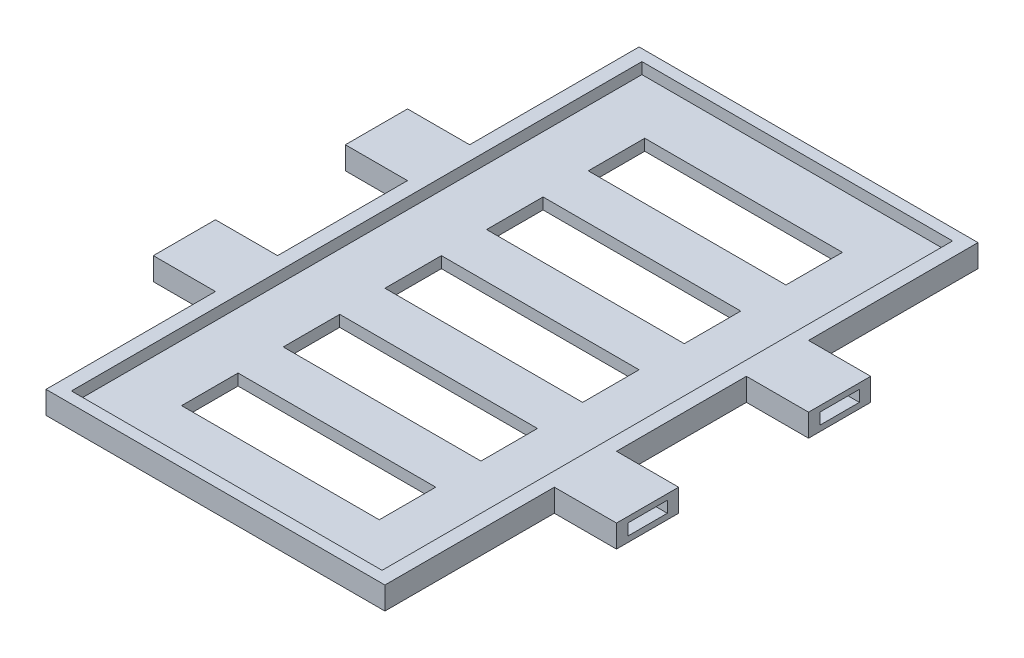
SolidWorks part; units mm, degrees
ref_plane "Alzado" through (0, 0, 0) normal (0, 0, 1) x (1, 0, 0)
ref_plane "Planta" through (0, 0, 0) normal (0, 1, 0) x (1, 0, 0)
ref_plane "Vista lateral" through (0, 0, 0) normal (1, 0, 0) x (0, 0, -1)
sketch "Croquis1" plane through (0, 0, 0) normal (0, 1, 0) x (1, 0, 0)
  line L0 (30, -52.5) -> (30, -22.5)
  line L1 (-30, 52.5) -> (30, 52.5)
  line L2 (30, -22.5) -> (30, -11.5) construction
  line L3 (-30, -52.5) -> (30, -52.5)
  line L4 (30, 11.5) -> (30, 22.5) construction
  line L5 (-30, 52.5) -> (30, -52.5) construction
  line L6 (-30, -52.5) -> (30, 52.5) construction
  line L7 (30, -22.5) -> (41, -22.5)
  line L8 (41, -22.5) -> (41, -11.5)
  line L9 (41, -11.5) -> (30, -11.5)
  line L10 (30, -11.5) -> (30, 11.5)
  line L11 (30, 11.5) -> (41, 11.5)
  line L12 (41, 11.5) -> (41, 22.5)
  line L13 (41, 22.5) -> (30, 22.5)
  line L14 (30, 22.5) -> (30, 52.5)
  line L15 (-30, 52.5) -> (-30, 22.5)
  line L16 (-30, 22.5) -> (-41, 22.5)
  line L17 (-41, 22.5) -> (-41, 11.5)
  line L18 (-41, 11.5) -> (-30, 11.5)
  line L19 (-30, 11.5) -> (-30, -11.5)
  line L20 (-30, -11.5) -> (-41, -11.5)
  line L21 (-41, -11.5) -> (-41, -22.5)
  line L22 (-41, -22.5) -> (-30, -22.5)
  line L23 (-30, -22.5) -> (-30, -52.5)
  line L24 (-30, 11.5) -> (-30, 22.5) construction
  line L25 (-30, -22.5) -> (-30, -11.5) construction
  point P0 (0, 0)
  dimension "D1" = 23
  dimension "D2" = 60
  dimension "D3" = 11
  dimension "D4" = 11
  dimension "D5" = 30
extrude "Saliente-Extruir1" add sketch "Croquis1" along normal blind 4
sketch "Croquis2" plane through (0, 4, 0) normal (0, 1, 0) x (1, 0, 0)
  line L0 (30, 52.5) -> (-30, 52.5) construction
  line L1 (-27.5, 50.5) -> (27.5, 50.5)
  line L2 (-27.5, 50.5) -> (-27.5, -50.5)
  line L3 (-27.5, -50.5) -> (27.5, -50.5)
  line L4 (27.5, 50.5) -> (27.5, -50.5)
  line L5 (-27.5, 50.5) -> (27.5, -50.5) construction
  line L6 (-27.5, -50.5) -> (27.5, 50.5) construction
  point P0 (0, 0)
  dimension "D1" = 2
  dimension "D2" = 55
extrude "Cortar-Extruir1" cut sketch "Croquis2" against normal blind 2
sketch "Croquis4" plane through (-41, 0, 0) normal (-1, 0, 0) x (0, 0, 1)
  line L0 (-22.5, 2) -> (-11.5, 2) construction
  line L2 (-20.5, 3) -> (-13.5, 3)
  line L3 (-20.5, 3) -> (-20.5, 1)
  line L4 (-20.5, 1) -> (-13.5, 1)
  line L5 (-22.5, 4) -> (-22.5, 0) construction
  line L6 (-11.5, 4) -> (-11.5, 0) construction
  line L7 (-17, 4) -> (-17, 0) construction
  line L8 (-22.5, 4) -> (-11.5, 4) construction
  line L9 (-22.5, 0) -> (-11.5, 0) construction
  line L10 (-13.5, 3) -> (-13.5, 1)
  line L11 (-20.5, 3) -> (-13.5, 1) construction
  line L12 (-20.5, 1) -> (-13.5, 3) construction
  point P0 (-17, 2)
  dimension "D1" = 7
  dimension "D2" = 2
extrude "Cortar-Extruir2" cut sketch "Croquis4" against normal blind 9
sketch "Croquis6" plane through (-41, 0, 0) normal (-1, 0, 0) x (0, 0, 1)
  line L0 (17, 4) -> (17, 0) construction
  line L1 (11.5, 4) -> (22.5, 4) construction
  line L2 (11.5, 0) -> (22.5, 0) construction
  line L4 (11.5, 4) -> (11.5, 0) construction
  line L5 (11.5, 2) -> (22.5, 2) construction
  line L6 (22.5, 4) -> (22.5, 0) construction
  line L7 (13.5, 3) -> (20.5, 3)
  line L8 (13.5, 3) -> (13.5, 1)
  line L9 (13.5, 1) -> (20.5, 1)
  line L10 (20.5, 3) -> (20.5, 1)
  line L11 (13.5, 3) -> (20.5, 1) construction
  line L12 (13.5, 1) -> (20.5, 3) construction
  point P6 (17, 2)
  dimension "D1" = 7
  dimension "D2" = 2
extrude "Cortar-Extruir3" cut sketch "Croquis6" against normal blind 9
sketch "Croquis7" plane through (41, 0, 0) normal (1, 0, 0) x (0, 0, -1)
  line L0 (-17, 0) -> (-17, 4) construction
  line L1 (-22.5, 0) -> (-11.5, 0) construction
  line L2 (-22.5, 4) -> (-11.5, 4) construction
  line L4 (-22.5, 4) -> (-22.5, 0) construction
  line L5 (-22.5, 2) -> (-11.5, 2) construction
  line L6 (-11.5, 4) -> (-11.5, 0) construction
  line L7 (-20.5, 1) -> (-13.5, 1)
  line L8 (-20.5, 1) -> (-20.5, 3)
  line L9 (-20.5, 3) -> (-13.5, 3)
  line L10 (-13.5, 1) -> (-13.5, 3)
  line L11 (-20.5, 1) -> (-13.5, 3) construction
  line L12 (-20.5, 3) -> (-13.5, 1) construction
  point P6 (-17, 2)
  dimension "D1" = 7
  dimension "D2" = 2
extrude "Cortar-Extruir4" cut sketch "Croquis7" against normal blind 9
sketch "Croquis8" plane through (41, 0, 0) normal (1, 0, 0) x (0, 0, -1)
  line L0 (17, 4) -> (17, 0) construction
  line L1 (11.5, 4) -> (22.5, 4) construction
  line L2 (11.5, 0) -> (22.5, 0) construction
  line L4 (11.5, 4) -> (11.5, 0) construction
  line L5 (11.5, 2) -> (22.5, 2) construction
  line L6 (22.5, 4) -> (22.5, 0) construction
  line L7 (13.5, 1) -> (20.5, 1)
  line L8 (13.5, 1) -> (13.5, 3)
  line L9 (13.5, 3) -> (20.5, 3)
  line L10 (20.5, 1) -> (20.5, 3)
  line L11 (13.5, 1) -> (20.5, 3) construction
  line L12 (13.5, 3) -> (20.5, 1) construction
  point P6 (17, 2)
  dimension "D1" = 7
  dimension "D2" = 2
extrude "Cortar-Extruir5" cut sketch "Croquis8" against normal blind 9
sketch "Croquis9" [suppressed] plane through (0, 0, 0) normal (0, 1, 0) x (1, 0, 0)
  line L0 (0, 0) -> (0, 50) construction
  line L1 (-105.9535, -48.7223) -> (-6.8702, -116.4165)
  line L2 (-105.9535, -48.7223) -> (6.8702, 116.4165)
  line L3 (6.8702, 116.4165) -> (105.9535, 48.7223)
  line L4 (-6.8702, -116.4165) -> (105.9535, 48.7223)
  line L5 (-105.9535, -48.7223) -> (105.9535, 48.7223) construction
  line L6 (6.8702, 116.4165) -> (-6.8702, -116.4165) construction
  point P0 (0, 0)
  point P6 (56.4118, 82.5694)
  dimension "D1" = 120
  dimension "D2" = 200
  dimension "D3" = 90
  dimension "D4" = 90
  dimension "D5" = 90
  dimension "D6" = 60
  dimension "D7" = 50
sketch "Croquis10" plane through (0, 0, 0) normal (0, 1, 0) x (1, 0, 0)
  line L0 (17.5, 31) -> (17.5, 23) construction
  line L1 (-17.5, 41) -> (17.5, 41)
  line L2 (-17.5, 41) -> (-17.5, 31)
  line L3 (-17.5, 31) -> (17.5, 31)
  line L4 (17.5, 41) -> (17.5, 31)
  line L5 (-17.5, 23) -> (17.5, 23)
  line L6 (-17.5, 23) -> (-17.5, 13)
  line L7 (-17.5, 13) -> (17.5, 13)
  line L8 (17.5, 23) -> (17.5, 13)
  line L9 (-17.5, 5) -> (17.5, 5)
  line L10 (-17.5, 5) -> (-17.5, -5)
  line L11 (-17.5, -5) -> (17.5, -5)
  line L12 (17.5, 5) -> (17.5, -5)
  line L13 (-17.5, -13) -> (17.5, -13)
  line L14 (-17.5, -13) -> (-17.5, -23)
  line L15 (-17.5, -23) -> (17.5, -23)
  line L16 (17.5, -13) -> (17.5, -23)
  line L17 (-17.5, -31) -> (17.5, -31)
  line L18 (-17.5, -31) -> (-17.5, -41)
  line L19 (-17.5, -41) -> (17.5, -41)
  line L20 (17.5, -31) -> (17.5, -41)
  line L21 (17.5, 13) -> (17.5, 5) construction
  line L22 (17.5, -5) -> (17.5, -13) construction
  line L23 (17.5, -23) -> (17.5, -31) construction
  line L24 (0, -5) -> (0, 5) construction
  point P22 (0, 0)
  dimension "D1" = 10
  dimension "D2" = 8
  dimension "D3" = 35
extrude "Cortar-Extruir6" cut sketch "Croquis10" along normal through all
